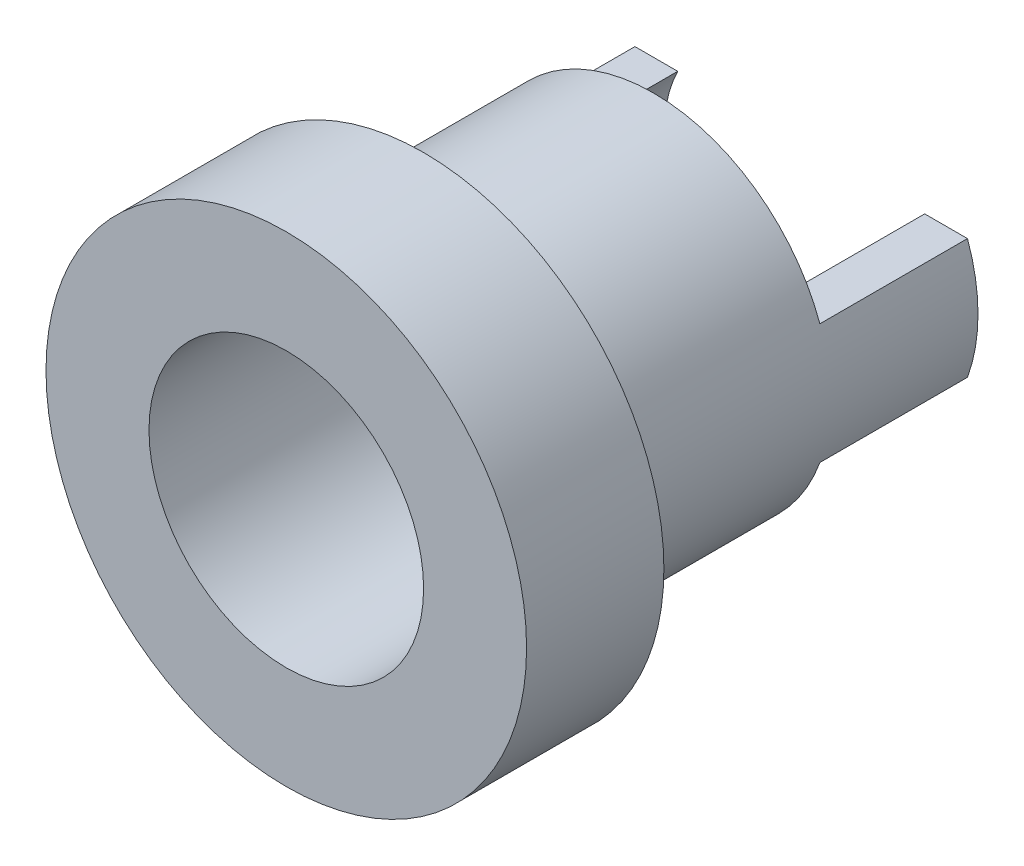
SolidWorks part; units mm, degrees
ref_plane "前视基准面" through (0, 0, 0) normal (0, 0, 1) x (1, 0, 0)
ref_plane "上视基准面" through (0, 0, 0) normal (0, 1, 0) x (1, 0, 0)
ref_plane "右视基准面" through (0, 0, 0) normal (1, 0, 0) x (0, 0, -1)
sketch "草图1" plane through (0, 0, 0) normal (0, 0, 1) x (1, 0, 0)
  circle A0 centre (0, 0) radius 7
  dimension "D1" = 14
extrude "凸台-拉伸1" add sketch "草图1" along normal blind 4
sketch "草图2" plane through (0, 0, 0) normal (0, 0, -1) x (-1, 0, 0)
  circle A0 centre (0, 0) radius 5.15
  dimension "D1" = 10.3
extrude "凸台-拉伸2" add sketch "草图2" along normal blind 11
sketch "草图3" plane through (0, 0, -11) normal (0, 0, -1) x (-1, 0, 0)
  circle A0 centre (0, 0) radius 4
  dimension "D1" = 8
extrude "切除-拉伸1" cut sketch "草图3" against normal through all both and the other way through all
sketch "草图4" plane through (0, 0, 4) normal (0, 0, 1) x (1, 0, 0)
  line L0 (0, 7) -> (0, -7) construction
  circle A0 centre (0, 0) radius 7 construction
  point P0 (0, 7)
  point P1 (0, -7)
  dimension "D1" = 14
sketch "草图5" plane through (0, 0, -11) normal (0, 0, -1) x (-1, 0, 0)
  line L0 (0, 0) -> (0, -5.15) construction
  circle A0 centre (0, 0) radius 5.15 construction
  point P0 (0, -5.15)
  point P1 (0, 0)
ref_plane "基准面1" through (0, 0, 0) normal (1, 0, 0) x (0, 0, -1)
sketch "草图6" plane through (0, 0, 0) normal (1, 0, 0) x (0, 0, -1)
  line L0 (11, 0) -> (2.5299, 0) construction
  line L1 (11, 5.15) -> (6.7, 5.15)
  line L2 (11, 5.15) -> (11, 1.75)
  line L3 (11, 1.75) -> (6.7, 1.75)
  line L4 (6.7, 5.15) -> (6.7, 1.75)
  line L9 (6.7, -5.15) -> (6.7, -1.75)
  line L10 (11, -5.15) -> (6.7, -5.15)
  line L11 (11, -5.15) -> (11, -1.75)
  line L12 (11, -1.75) -> (6.7, -1.75)
  point P0 (11, 5.15)
  dimension "D1" = 3.5
  dimension "D2" = 4.3
extrude "切除-拉伸2" cut sketch "草图6" against normal through all both and the other way through all
